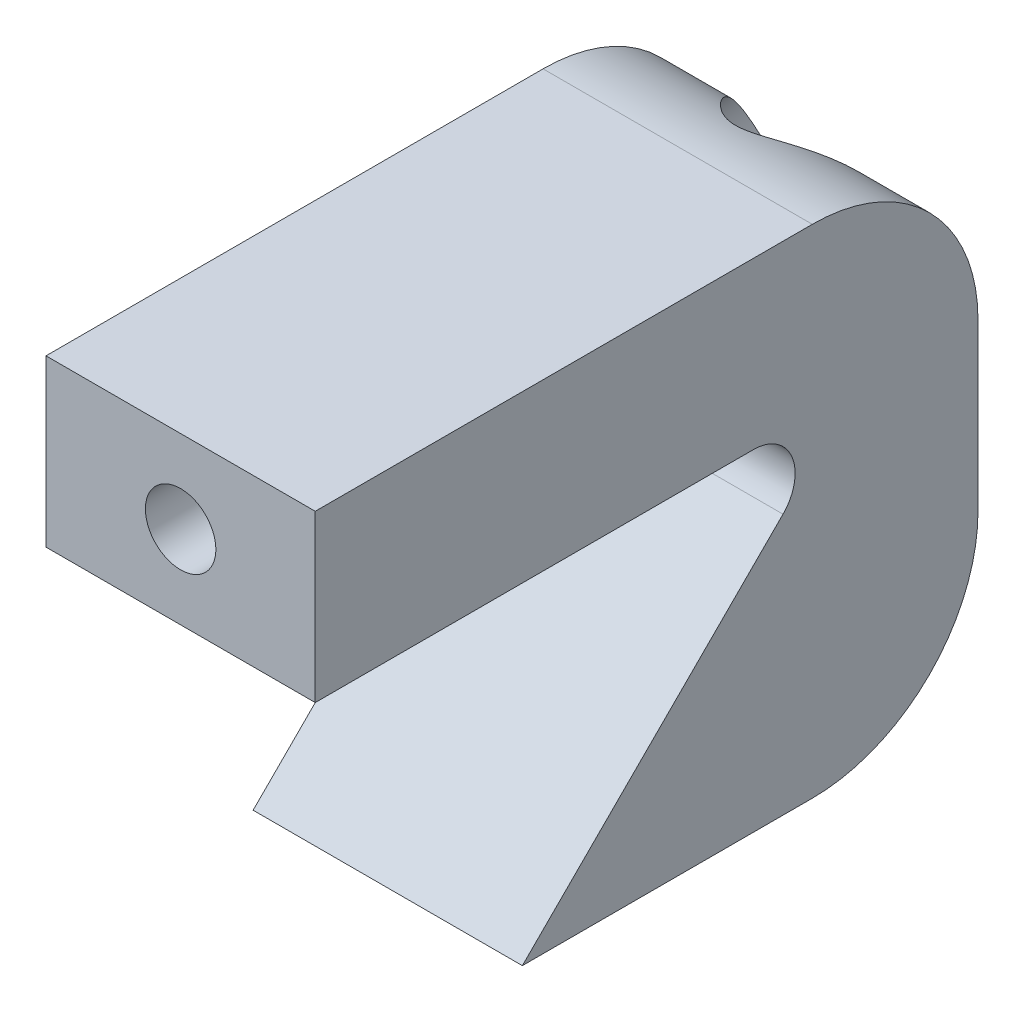
SolidWorks part; units mm, degrees
ref_plane "Płaszczyzna przednia" through (0, 0, 0) normal (0, 0, 1) x (1, 0, 0)
ref_plane "Płaszczyzna górna" through (0, 0, 0) normal (0, 1, 0) x (1, 0, 0)
ref_plane "Płaszczyzna prawa" through (0, 0, 0) normal (1, 0, 0) x (0, 0, -1)
sketch "Sketch1" plane through (0, 0, 0) normal (1, 0, 0) x (0, 0, -1)
  line L1 (0, -16) -> (-16, -16)
  line L2 (-16, -16) -> (0, 0)
  line L3 (0, -16) -> (6, -16)
  line L4 (6, -16) -> (6, 8)
  line L5 (6, 8) -> (-26, 8)
  line L6 (-26, 8) -> (-26, 0)
  line L7 (-26, 0) -> (0, 0)
  line L9 (0, 0) -> (0, -16) construction
  dimension "D1" = 16
  dimension "D2" = 16
  dimension "D3" = 6
  dimension "D4" = 24
  dimension "D5" = 32
  dimension "D6" = 8
  dimension "D7" = 26
extrude "Boss-Extrude1" add sketch "Sketch1" along normal blind 13
fillet "Fillet2" radius 8 2 edges at (6.5, 8, -6) (6.5, -16, -6)
sketch "Sketch2" plane through (0, 0, -6) normal (0, 0, -1) x (-1, 0, 0)
  line L1 (-13, 8) -> (0, 8) construction
  line L2 (-13, 8) -> (-13, 0) construction
  line L3 (-13, 0) -> (0, 0) construction
  line L4 (0, 8) -> (0, 0) construction
  line L5 (-13, 8) -> (0, 0) construction
  line L6 (-13, 0) -> (0, 8) construction
  circle A0 centre (-6.5, 4) radius 1.7
  point P4 (-6.5, 4)
  dimension "D1" = 13
  dimension "D2" = 8
extrude "Cut-Extrude1" cut sketch "Sketch2" against normal blind 41
sketch "Sketch3" plane through (0, 0, -6) normal (0, 0, -1) x (-1, 0, 0)
  circle A0 centre (-6.5, 4) radius 3.5
extrude "Cut-Extrude2" cut sketch "Sketch3" against normal blind 28
sketch "Sketch6" plane through (0, 0, 22) normal (0, 0, -1) x (-1, 0, 0)
  point P1 (-6.5, 4)
  point P6 (0, 0)
hole_wizard "CSK for M3 Countersunk Flat Head Screw1" positions "Sketch6" profile "Sketch5" countersink size "M3" standard "ISO" end condition through all
sketch "Sketch5" plane through (6.5, 4, 22) normal (1, 0, 0) x (0, 1, 0)
  line L0 (0, 0) -> (0, 4)
  line L1 (0, 4) -> (1.6, 4)
  line L2 (1.6, 4) -> (1.6, 1.55)
  line L3 (1.6, 1.55) -> (3.15, 0)
  line L5 (3.15, 0) -> (0, 0)
  line L6 (-1.6, 1.55) -> (-3.15, 0) construction
  line L11 (0, -6.35) -> (0, 107.95) construction
  dimension "Thru Hole Dia." = 3.2
  dimension "Thru Hole Depth" = 4
  dimension "Near C'Sink Dia." = 6.3
  dimension "Near C'Sink Angle" = 90
fillet "Fillet3" radius 2 1 edges at (6.5, 0, 0)
